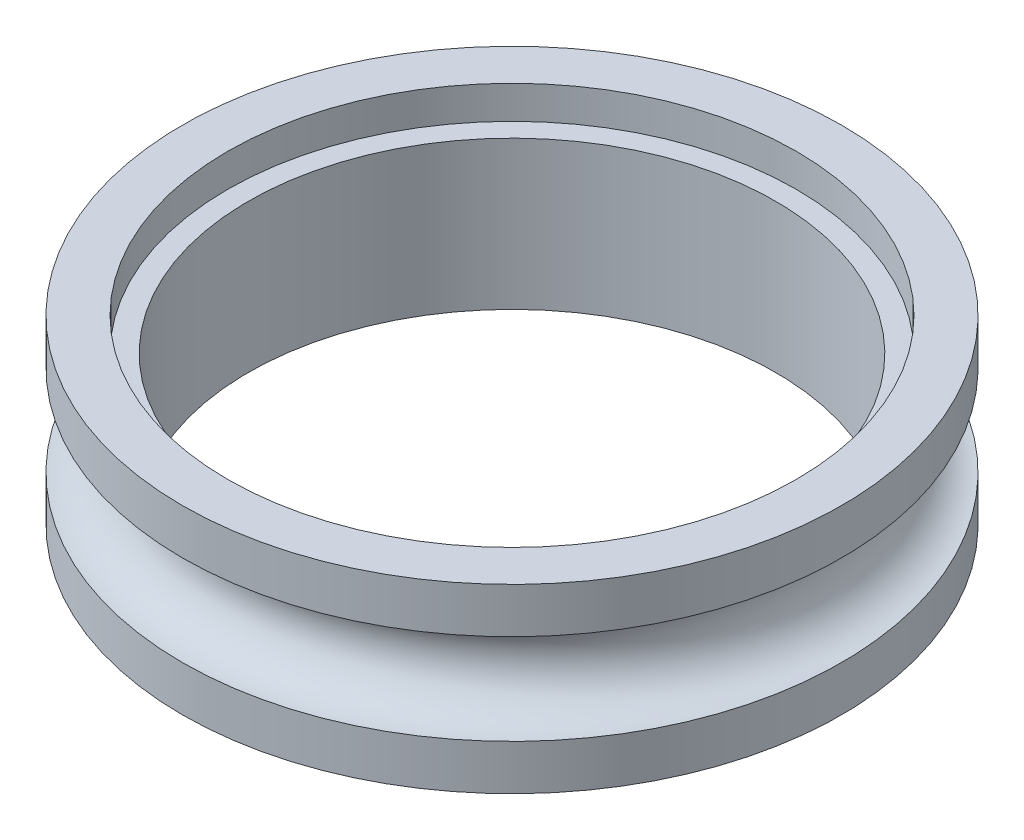
SolidWorks part; units mm, degrees
ref_plane "Front Plane" through (0, 0, 0) normal (0, 0, 1) x (1, 0, 0)
ref_plane "Top Plane" through (0, 0, 0) normal (0, 1, 0) x (1, 0, 0)
ref_plane "Right Plane" through (0, 0, 0) normal (1, 0, 0) x (0, 0, -1)
sketch "Sketch1" plane through (0, 0, 0) normal (0, 1, 0) x (1, 0, 0)
  circle A0 centre (0, 0) radius 10.16
  dimension "D1" = 20.32
extrude "Boss-Extrude1" add sketch "Sketch1" along normal blind 5.588
sketch "Sketch2" plane through (0, 0, 0) normal (0, 0, 1) x (1, 0, 0)
  line L0 (-10.16, 5.588) -> (-10.16, 0) construction
  line L2 (-10.16, 4.191) -> (-10.16, 1.397)
  line L3 (0, 5.588) -> (0, 0) construction
  line L4 (10.16, 5.588) -> (-10.16, 5.588) construction
  line L5 (-10.16, 0) -> (10.16, 0) construction
  arc A0 (-10.16, 4.191) -> (-10.16, 1.397) centre (-10.16, 2.794) cw
  point P3 (0, 0)
  point P6 (0, 2.794)
  point P7 (0, 0)
  dimension "D1" = 1.397
revolve "Cut-Revolve1" cut sketch "Sketch2" angle 360 about L3
sketch "Sketch3" plane through (0, 5.588, 0) normal (0, 1, 0) x (1, 0, 0)
  circle A1 centre (0, 0) radius 8.128
  dimension "D1" = 16.256
extrude "Cut-Extrude1" cut sketch "Sketch3" against normal blind 10.16
sketch "Sketch4" plane through (0, 5.588, 0) normal (0, 1, 0) x (1, 0, 0)
  circle A0 centre (0, 0) radius 8.763
  dimension "D1" = 17.526
extrude "Cut-Extrude2" cut sketch "Sketch4" against normal blind 1.016
